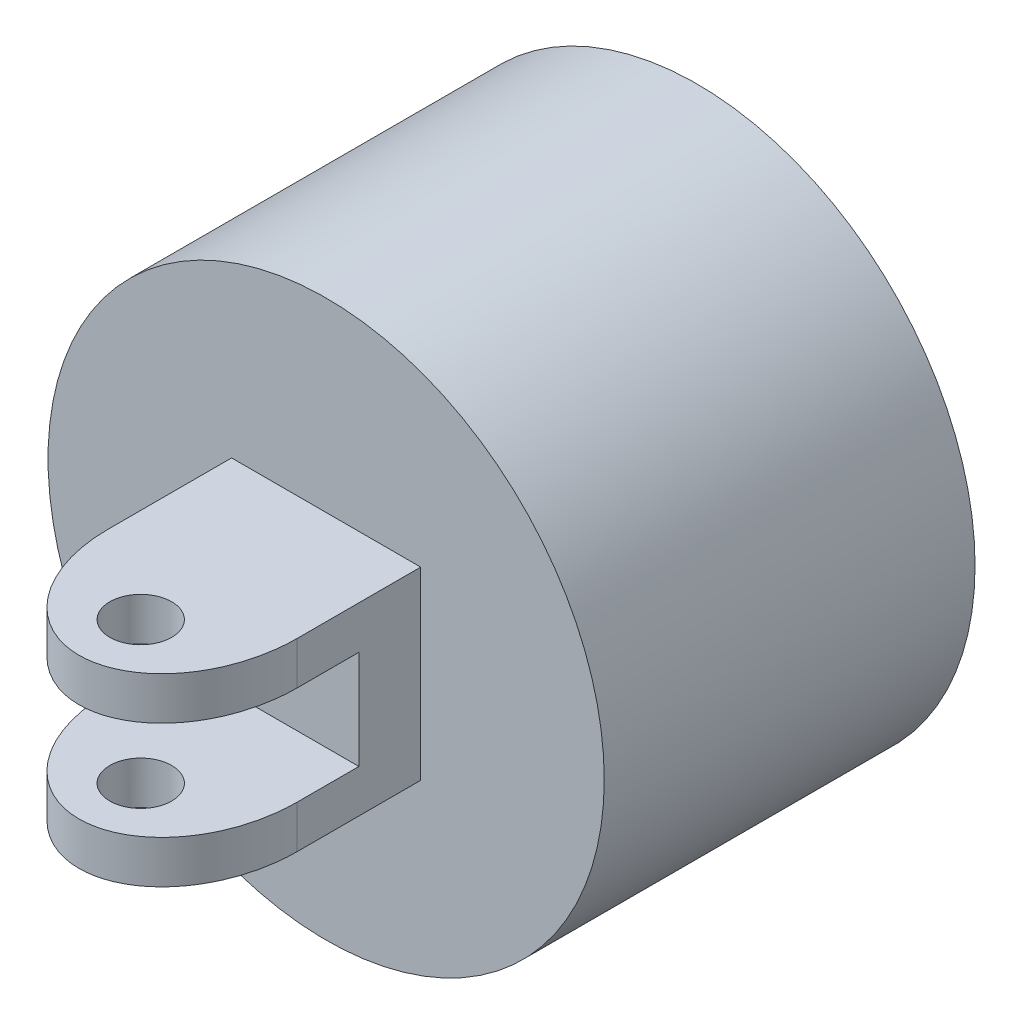
SolidWorks part; units mm, degrees
ref_plane "Front Plane" through (0, 0, 0) normal (0, 0, 1) x (1, 0, 0)
ref_plane "Top Plane" through (0, 0, 0) normal (0, 1, 0) x (1, 0, 0)
ref_plane "Right Plane" through (0, 0, 0) normal (1, 0, 0) x (0, 0, -1)
sketch "Sketch1" plane through (0, 0, 0) normal (0, 0, 1) x (1, 0, 0)
  circle A0 centre (0, 0) radius 22.5
  dimension "D1" = 45
extrude "Boss-Extrude1" add sketch "Sketch1" along normal blind 30
sketch "Sketch2" plane through (0, 0, 0) normal (0, 0, -1) x (-1, 0, 0)
  line L0 (-1.5, -15) -> (1.5, -15)
  line L1 (15, -1.5) -> (-15, -1.5)
  line L2 (15, -1.5) -> (15, 1.5)
  line L3 (15, 1.5) -> (-15, 1.5)
  line L4 (-15, -1.5) -> (-15, 1.5)
  line L5 (15, -1.5) -> (-15, 1.5) construction
  line L6 (15, 1.5) -> (-15, -1.5) construction
  line L7 (-1.5, -15) -> (-1.5, 15)
  line L8 (-1.5, 15) -> (1.5, 15)
  line L9 (1.5, -15) -> (1.5, 15)
  line L10 (-15, 1.5) -> (-15, -1.5)
  line L11 (-15, 1.5) -> (15, 1.5)
  line L12 (15, 1.5) -> (15, -1.5)
  line L13 (-15, -1.5) -> (15, -1.5)
  line L14 (1.5, 15) -> (-1.5, 15)
  line L15 (1.5, 15) -> (1.5, -15)
  line L16 (1.5, -15) -> (-1.5, -15)
  line L17 (-1.5, 15) -> (-1.5, -15)
  circle A0 centre (0, 0) radius 7.5
  point P22 (0, 0)
  dimension "D1" = 15
  dimension "D2" = 30
  dimension "D3" = 3
  dimension "D5" = 15
  dimension "D6" = 15.0748
  dimension "D4" = 4
extrude "Cut-Extrude1" cut sketch "Sketch2" against normal blind 10 contours A0 L15 L8 L17 | L9 A0 L7 L3 | L7 A0 L3 | L11 A0 L9 | L1 A0 L17 | L15 A0 L13
sketch "Sketch3" plane through (0, 0, 30) normal (0, 0, 1) x (1, 0, 0)
  line L1 (7.6498, -7.4691) -> (-7.6498, -7.4691)
  line L2 (7.6498, -7.4691) -> (7.6498, 7.4691)
  line L3 (7.6498, 7.4691) -> (-7.6498, 7.4691)
  line L4 (-7.6498, -7.4691) -> (-7.6498, 7.4691)
  line L5 (7.6498, -7.4691) -> (-7.6498, 7.4691) construction
  line L6 (7.6498, 7.4691) -> (-7.6498, -7.4691) construction
  point P0 (0, 0)
extrude "Boss-Extrude2" add sketch "Sketch3" along normal blind 20
sketch "Sketch4" plane through (-7.6498, 0, 0) normal (-1, 0, 0) x (0, 0, 1)
  line L0 (50, 0) -> (30, 0) construction
  line L1 (50, 7.4691) -> (50, -7.4691) construction
  line L2 (30, 7.4691) -> (30, -7.4691) construction
  line L4 (40, 4) -> (50, 4)
  line L5 (50, 4) -> (50, 0)
  line L6 (50, 0) -> (50, -4)
  line L7 (50, -4) -> (40, -4)
  line L8 (40, -4) -> (35, -4)
  line L9 (35, -4) -> (35, 4)
  line L10 (35, 4) -> (40, 4)
  dimension "D1" = 10
  dimension "D2" = 5
  dimension "D3" = 8
  dimension "D4" = 10
  dimension "D5" = 4
extrude "Cut-Extrude2" cut sketch "Sketch4" against normal blind 20
sketch "Sketch5" plane through (0, 7.4691, 0) normal (0, 1, 0) x (1, 0, 0)
  line L1 (0, -50) -> (0, -30) construction
  line L2 (7.6498, -50) -> (-7.6498, -50) construction
  line L3 (7.6498, -30) -> (-7.6498, -30) construction
  line L4 (0, -40) -> (7.6498, -40) construction
  line L5 (7.6498, -50) -> (7.6498, -30) construction
  line L6 (3.8249, -40) -> (3.8249, -50) construction
  line L7 (3.8249, -45) -> (0, -45) construction
  line L8 (3.8249, -45) -> (7.6498, -45) construction
  line L9 (7.6498, -40) -> (7.6498, -50)
  line L10 (7.6498, -50) -> (0, -50)
  line L11 (0, -50) -> (-7.6498, -50)
  line L12 (-7.6498, -50) -> (-7.6498, -40)
  circle A0 centre (0, -45) radius 2.5
  ellipse E0 centre (0, -40) end of major axis (0, -30) minor radius 7.6498 (-7.6498, -40) -> (7.6498, -40) ccw
  line M4 (-7.6498, -30) -> (-7.6498, -50)
  line M5 (-7.6498, -50) -> (7.6498, -50)
  line M6 (7.6498, -50) -> (7.6498, -30)
  dimension "D1" = 5
extrude "Cut-Extrude4" cut sketch "Sketch5" against normal blind 20 contours A0 | E0 M5 M6 | E0 M4 M5
